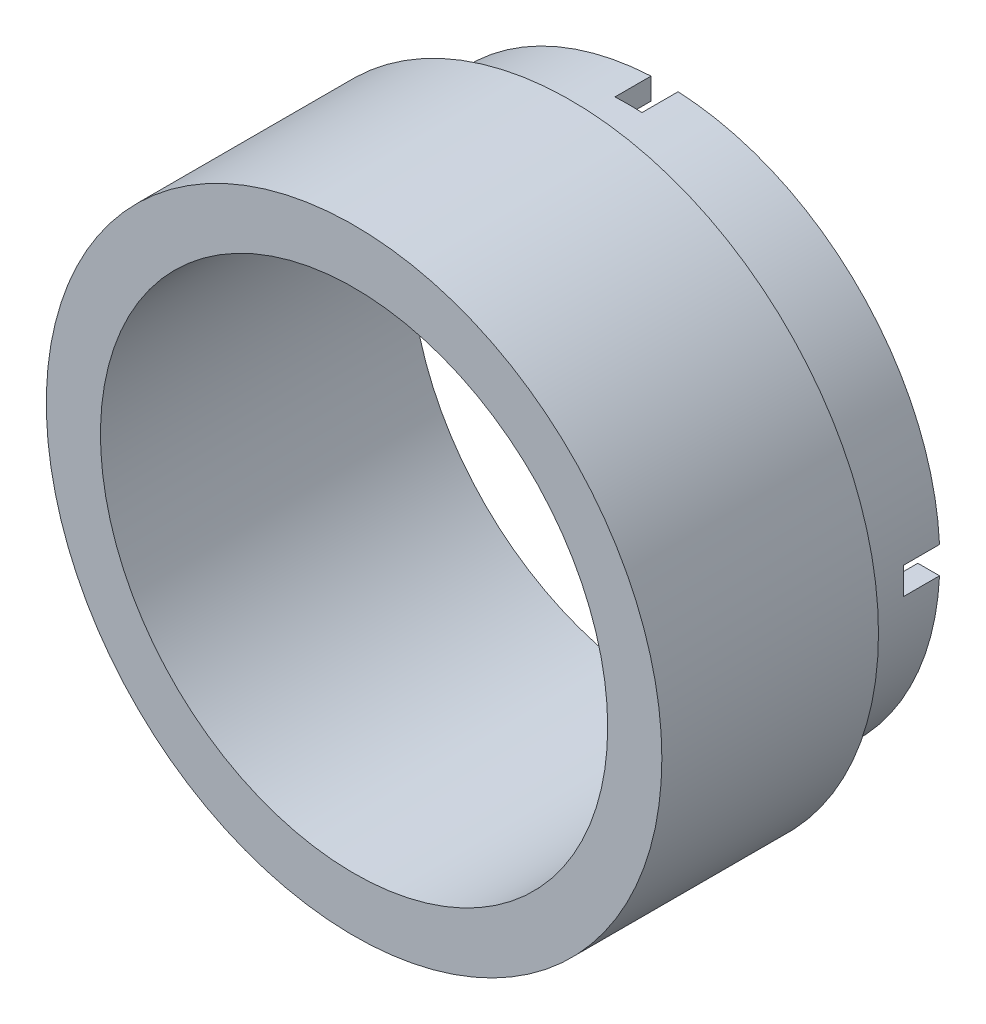
SolidWorks part; units mm, degrees
ref_plane "Front Plane" through (0, 0, 0) normal (0, 0, 1) x (1, 0, 0)
ref_plane "Top Plane" through (0, 0, 0) normal (0, 1, 0) x (1, 0, 0)
ref_plane "Right Plane" through (0, 0, 0) normal (1, 0, 0) x (0, 0, -1)
sketch "Sketch1" plane through (0, 0, 0) normal (0, 0, 1) x (1, 0, 0)
  circle A0 centre (0, 0) radius 15.25
  circle A1 centre (0, 0) radius 14.05
  dimension "D1" = 30.5
  dimension "D2" = 1.2
extrude "Boss-Extrude1" add sketch "Sketch1" along normal blind 5.2
sketch "Sketch2" plane through (0, 0, 0) normal (0, 0, 1) x (1, 0, 0)
  line L1 (-0.75, 17.4513) -> (0.75, 17.4513)
  line L2 (-0.75, 17.4513) -> (-0.75, 0.75)
  line L3 (-0.75, -17.4513) -> (0.75, -17.4513)
  line L4 (0.75, 17.4513) -> (0.75, 0.75)
  line L5 (-0.75, 17.4513) -> (0.75, -17.4513) construction
  line L6 (-0.75, -17.4513) -> (0.75, 17.4513) construction
  line L7 (-21.8765, -0.75) -> (-0.75, -0.75)
  line L8 (-21.8765, -0.75) -> (-21.8765, 0.75)
  line L9 (-21.8765, 0.75) -> (-0.75, 0.75)
  line L10 (21.8765, -0.75) -> (21.8765, 0.75)
  line L11 (-21.8765, -0.75) -> (21.8765, 0.75) construction
  line L12 (-21.8765, 0.75) -> (21.8765, -0.75) construction
  line L14 (-0.75, -0.75) -> (-0.75, -17.4513)
  line L15 (0.75, -0.75) -> (0.75, -17.4513)
  line L17 (0.75, 0.75) -> (21.8765, 0.75)
  line L19 (0.75, -0.75) -> (21.8765, -0.75)
  point P0 (0, 0)
  point P6 (0, 0)
  dimension "D1" = 1.5
  dimension "D2" = 1.5
extrude "Cut-Extrude1" cut sketch "Sketch2" along normal blind 2
sketch "Sketch4" plane through (0, 0, 5.2) normal (0, 0, 1) x (1, 0, 0)
  circle A0 centre (0, 0) radius 14.05 construction
  circle A1 centre (0, 0) radius 14.05
  circle A2 centre (0, 0) radius 17.05
  dimension "D1" = 3
extrude "Boss-Extrude2" add sketch "Sketch4" along normal blind 12
